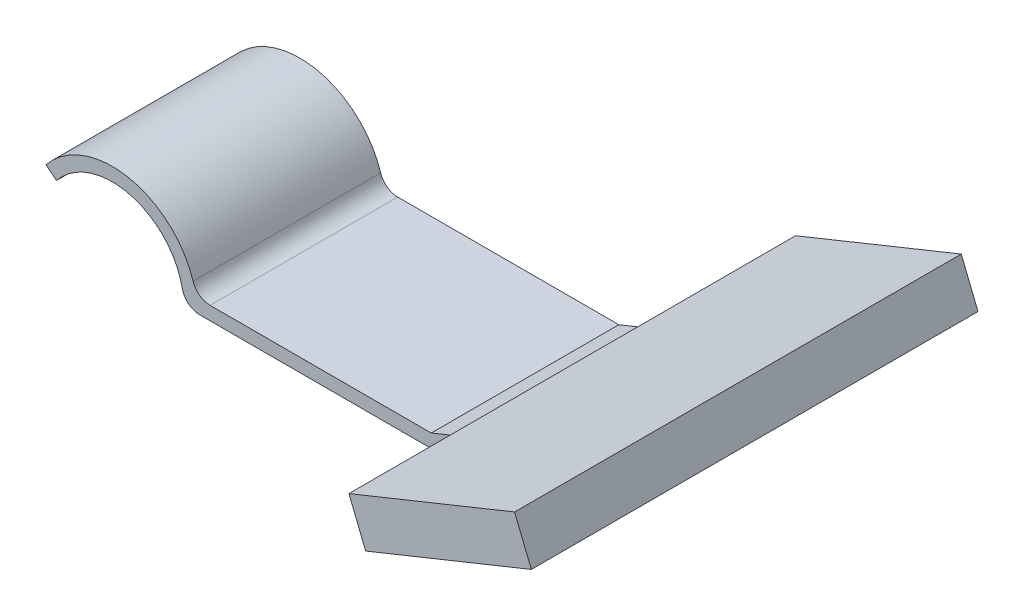
SolidWorks part; units mm, degrees
ref_plane "Front Plane" through (0, 0, 0) normal (0, 0, 1) x (1, 0, 0)
ref_plane "Top Plane" through (0, 0, 0) normal (0, 1, 0) x (1, 0, 0)
ref_plane "Right Plane" through (0, 0, 0) normal (1, 0, 0) x (0, 0, -1)
sketch "Sketch1" plane through (0, 0, 0) normal (0, 0, 1) x (1, 0, 0)
  line L0 (0, 0) -> (28, 0)
  line L1 (28, 0) -> (52.755, 10)
  arc A0 (0, 0) -> (-14.245, 5) centre (-8, 0) ccw
  dimension "D1" = 8
  dimension "D2" = 67
  dimension "D3" = 28
  dimension "D4" = 5
  dimension "D5" = 10
extrude "Extrude-Thin1" add sketch "Sketch1" along normal mid plane 21 thin thin type one direction wall 1.5
fillet "Fillet1" radius 2 1 edges at (0, 0, 0)
fillet "Fillet2" radius 2 1 edges at (1.3808, 1.5, 0)
sketch "Sketch3" plane through (48.8269, 19.724, 0) normal (0.9272, 0.3746, 0) x (0, 0, -1)
  line L0 (0, -8.9875) -> (0, -10.4875) construction
  line L1 (-10.5, -8.9875) -> (10.5, -8.9875) construction
  line L2 (-10.5, -10.4875) -> (10.5, -10.4875) construction
  line L4 (25, -12.2375) -> (-25, -12.2375)
  line L5 (25, -12.2375) -> (25, -7.2375)
  line L6 (25, -7.2375) -> (-25, -7.2375)
  line L7 (-25, -12.2375) -> (-25, -7.2375)
  line L8 (25, -12.2375) -> (-25, -7.2375) construction
  line L9 (25, -7.2375) -> (-25, -12.2375) construction
  point P6 (0, -9.7375)
  dimension "D1" = 5
  dimension "D2" = 50
extrude "Boss-Extrude1" add sketch "Sketch3" against normal blind 20
